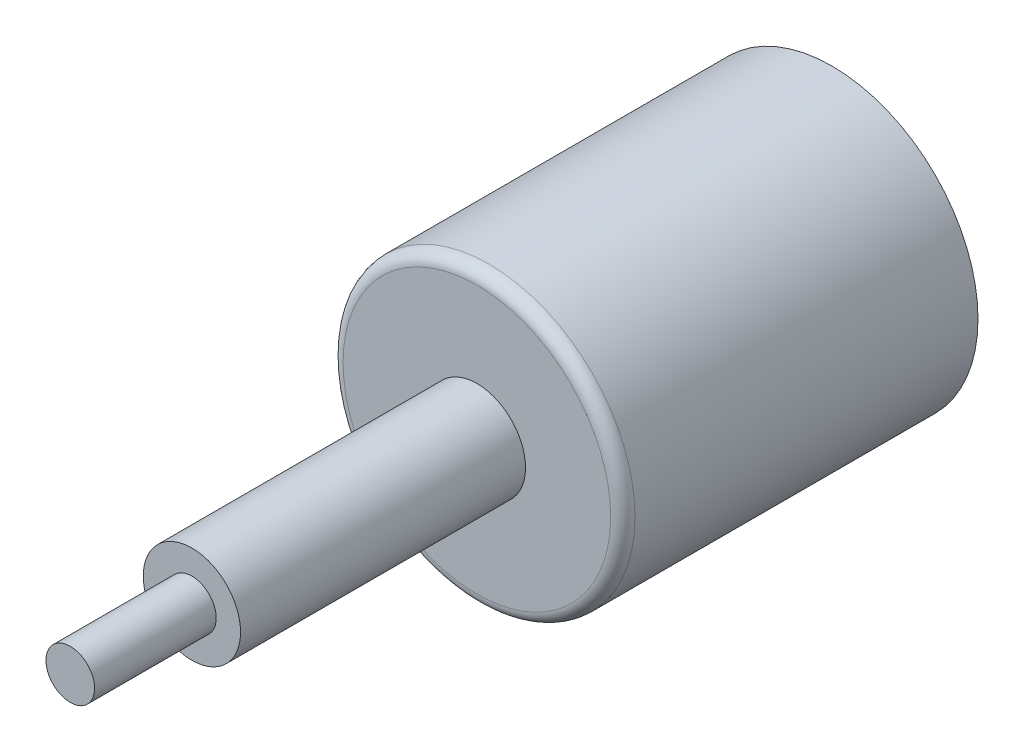
SolidWorks part; units mm, degrees
ref_plane "Plan de face" through (0, 0, 0) normal (0, 0, 1) x (1, 0, 0)
ref_plane "Plan de dessus" through (0, 0, 0) normal (0, 1, 0) x (1, 0, 0)
ref_plane "Plan de droite" through (0, 0, 0) normal (1, 0, 0) x (0, 0, -1)
sketch "Esquisse1" plane through (0, 0, 0) normal (0, 0, 1) x (1, 0, 0)
  circle A0 centre (0, 0) radius 12
extrude "Extrusion1" add sketch "Esquisse1" along normal blind 29.2
fillet "Congé1" radius 1 1 edges at (12, 0, 29.2)
sketch "Esquisse2" plane through (0, 0, 29.2) normal (0, 0, 1) x (1, 0, 0)
  circle A0 centre (0, 0) radius 4
extrude "Extrusion2" add sketch "Esquisse2" along normal blind 23.43
sketch "Esquisse3" plane through (0, 0, 52.63) normal (0, 0, 1) x (1, 0, 0)
  circle A0 centre (0, 0) radius 2
extrude "Extrusion3" add sketch "Esquisse3" along normal blind 10
